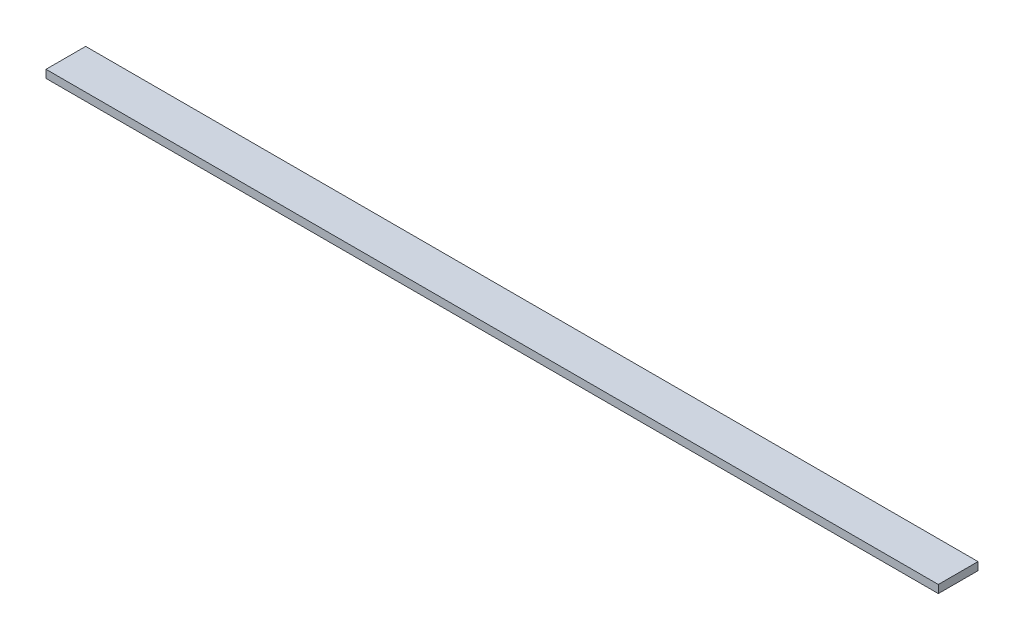
SolidWorks part; units mm, degrees
ref_plane "Спереди" through (0, 0, 0) normal (0, 0, 1) x (1, 0, 0)
ref_plane "Сверху" through (0, 0, 0) normal (0, 1, 0) x (1, 0, 0)
ref_plane "Справа" through (0, 0, 0) normal (1, 0, 0) x (0, 0, -1)
sketch "Эскиз1" plane through (0, 0, 0) normal (1, 0, 0) x (0, 0, -1)
  line L0 (0, 0) -> (20, 0)
extrude "Вытянуть-Тонкостенный1" add sketch "Эскиз1" along normal blind 450 thin
